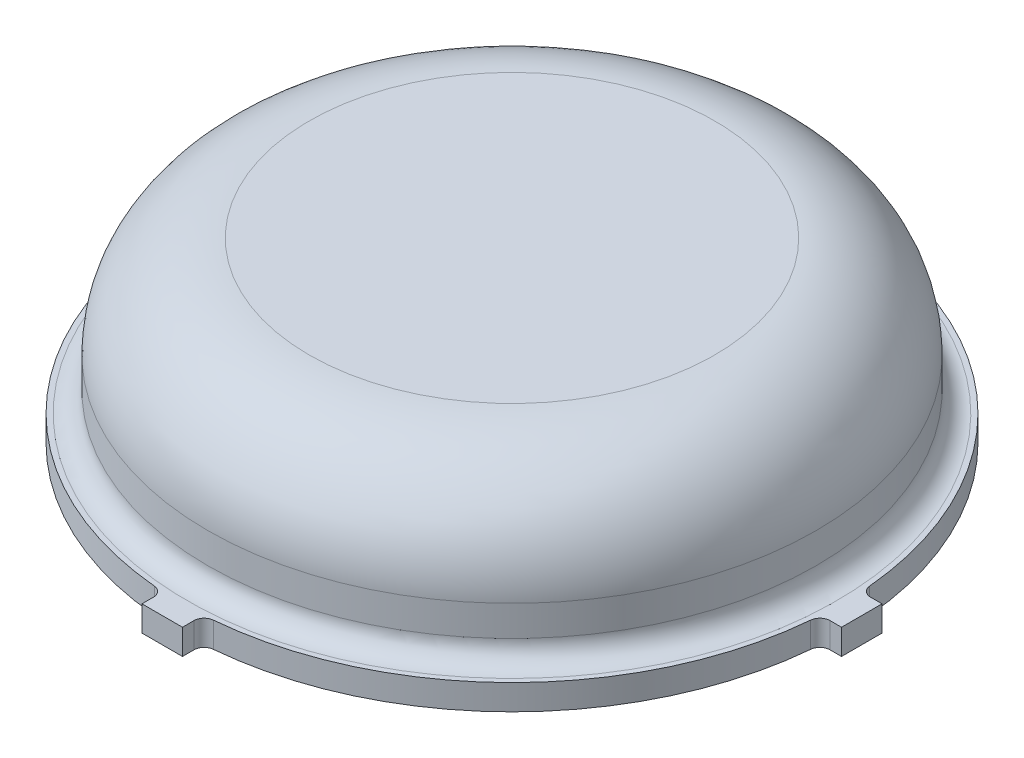
SolidWorks part; units mm, degrees
ref_plane "Front Plane" through (0, 0, 0) normal (0, 0, 1) x (1, 0, 0)
ref_plane "Top Plane" through (0, 0, 0) normal (0, 1, 0) x (1, 0, 0)
ref_plane "Right Plane" through (0, 0, 0) normal (1, 0, 0) x (0, 0, -1)
sketch "Sketch1" plane through (0, 0, 0) normal (0, 1, 0) x (1, 0, 0)
  circle A0 centre (0, 0) radius 38.1
  dimension "D1" = 76.2
extrude "Boss-Extrude1" add sketch "Sketch1" along normal blind 19.05
fillet "Fillet1" radius 12.7 1 edges at (0, 19.05, 38.1)
sketch "Sketch2" plane through (0, 0, 0) normal (0, -1, 0) x (1, 0, 0)
  circle A0 centre (0, 0) radius 41.275
  dimension "D1" = 82.55
extrude "Boss-Extrude2" add sketch "Sketch2" along normal blind 3.175
shell "Shell2" thickness 2.54
fillet "Fillet2" radius 2.54 1 edges at (0, 0, 38.1)
sketch "Sketch27" plane through (0, -3.175, 0) normal (0, -1, 0) x (1, 0, 0)
  line L0 (-41.275, 0) -> (41.275, 0)
  line L1 (0, 41.275) -> (0, -41.275)
  line L3 (-38.735, 2.54) -> (-43.815, 2.54)
  line L4 (-38.735, 2.54) -> (-38.735, -2.54)
  line L5 (-38.735, -2.54) -> (-43.815, -2.54)
  line L6 (-43.815, 2.54) -> (-43.815, -2.54)
  line L7 (-38.735, 2.54) -> (-43.815, -2.54) construction
  line L8 (-38.735, -2.54) -> (-43.815, 2.54) construction
  line L9 (-2.54, 38.735) -> (2.54, 38.735)
  line L10 (-2.54, 38.735) -> (-2.54, 43.815)
  line L11 (-2.54, 43.815) -> (2.54, 43.815)
  line L12 (2.54, 38.735) -> (2.54, 43.815)
  line L13 (-2.54, 38.735) -> (2.54, 43.815) construction
  line L14 (-2.54, 43.815) -> (2.54, 38.735) construction
  line L15 (38.735, 2.54) -> (43.815, 2.54)
  line L16 (38.735, 2.54) -> (38.735, -2.54)
  line L17 (38.735, -2.54) -> (43.815, -2.54)
  line L18 (43.815, 2.54) -> (43.815, -2.54)
  line L19 (38.735, 2.54) -> (43.815, -2.54) construction
  line L20 (38.735, -2.54) -> (43.815, 2.54) construction
  line L21 (-2.54, -38.735) -> (2.54, -38.735)
  line L22 (-2.54, -38.735) -> (-2.54, -43.815)
  line L23 (-2.54, -43.815) -> (2.54, -43.815)
  line L24 (2.54, -38.735) -> (2.54, -43.815)
  line L25 (-2.54, -38.735) -> (2.54, -43.815) construction
  line L26 (-2.54, -43.815) -> (2.54, -38.735) construction
  circle A0 centre (0, 0) radius 41.275 construction
  dimension "D1" = 5.08
  dimension "D2" = 5.08
  dimension "D3" = 5.08
  dimension "D4" = 5.08
  dimension "D5" = 5.08
  dimension "D6" = 5.08
  dimension "D7" = 5.08
  dimension "D8" = 5.08
extrude "Boss-Extrude12" add sketch "Sketch27" against normal blind 3.175 contours L11 L12 L9 L10 | L18 L17 L16 L15 | L24 L23 L22 L21 | L3 L6 L5 L4
fillet "Fillet3" radius 1.27 8 edges at (41.1968, -1.5875, 2.54) (-2.54, -1.5875, 41.1968) (-41.1968, -1.5875, 2.54) (-41.1968, -1.5875, -2.54) (-2.54, -1.5875, -41.1968) (2.54, -1.5875, -41.1968) (41.1968, -1.5875, -2.54) (2.54, -1.5875, 41.1968)
sketch "Sketch28" plane through (0, -2.54, 0) normal (0, -1, 0) x (1, 0, 0)
  circle A0 centre (0, 0) radius 35.56
  circle A1 centre (0, 0) radius 38.735
extrude "Boss-Extrude16" add sketch "Sketch28" along normal up to vertex (0.635 mm away)
sketch "Sketch31" plane through (0, 16.51, 0) normal (0, -1, 0) x (1, 0, 0)
  circle A0 centre (0, 0) radius 6
  circle A1 centre (0, 0) radius 4.5
  dimension "D1" = 12
  dimension "D2" = 9
extrude "Boss-Extrude17" add sketch "Sketch31" along normal up to surface (19.685 mm away) up to face at (0, -3.175, 0)
fillet "Fillet4" radius 8.89 1 edges at (0, 16.51, 6)
sketch "Sketch32" plane through (0, -3.175, 0) normal (0, -1, 0) x (1, 0, 0)
  circle A0 centre (0, 0) radius 6
extrude "Boss-Extrude18" add sketch "Sketch32" against normal blind 1.27
fillet "Fillet5" radius 2.54 1 edges at (0, -1.905, -4.5)
